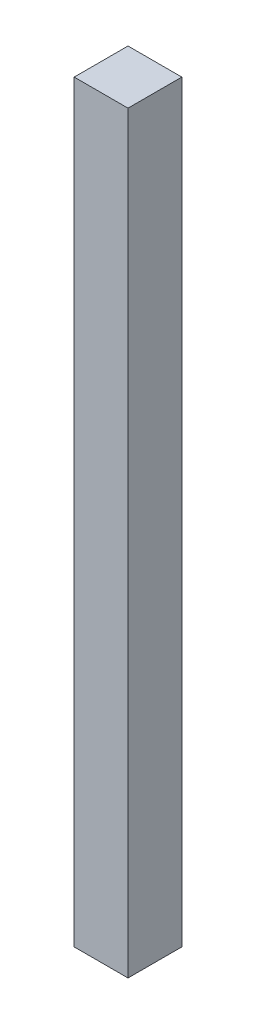
SolidWorks part; units mm, degrees
material "Plain Carbon Steel"
ref_plane "Front Plane" through (0, 0, 0) normal (0, 0, 1) x (1, 0, 0)
ref_plane "Top Plane" through (0, 0, 0) normal (0, 1, 0) x (1, 0, 0)
ref_plane "Right Plane" through (0, 0, 0) normal (1, 0, 0) x (0, 0, -1)
sketch "Sketch1" plane through (0, 0, 0) normal (0, 1, 0) x (1, 0, 0)
  line L1 (0, 0) -> (5, 0)
  line L2 (0, 0) -> (0, -5)
  line L3 (0, -5) -> (5, -5)
  line L4 (5, 0) -> (5, -5)
  dimension "D1" = 5
  dimension "D2" = 5
extrude "Boss-Extrude1" add sketch "Sketch1" along normal blind 70
